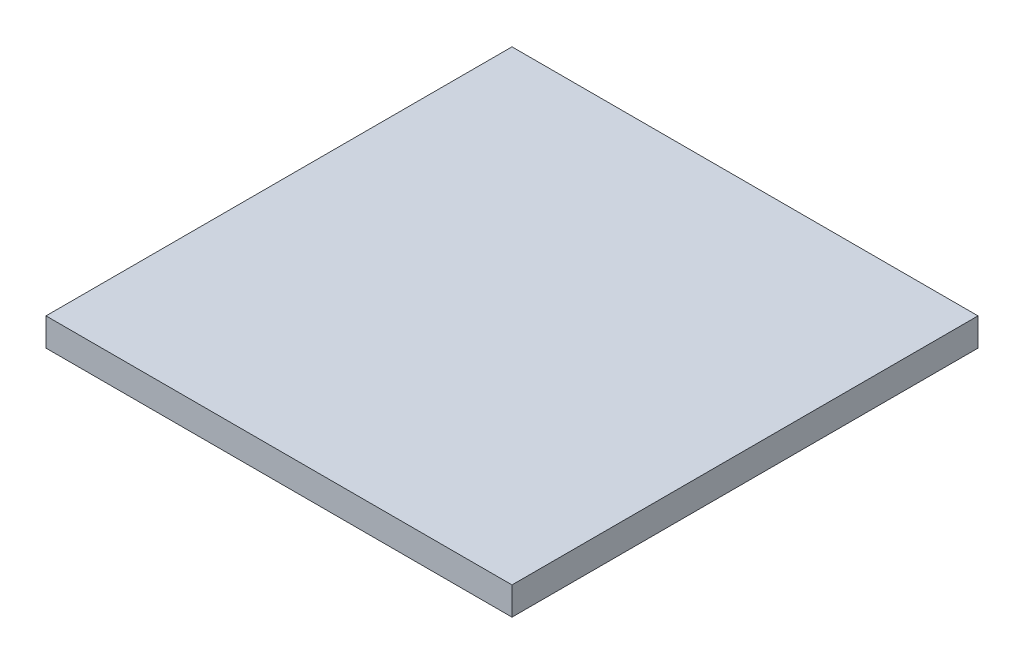
SolidWorks part; units mm, degrees
ref_plane "Front Plane" through (0, 0, 0) normal (0, 0, 1) x (1, 0, 0)
ref_plane "Top Plane" through (0, 0, 0) normal (0, 1, 0) x (1, 0, 0)
ref_plane "Right Plane" through (0, 0, 0) normal (1, 0, 0) x (0, 0, -1)
sketch "Sketch1" plane through (0, 0, 0) normal (0, 1, 0) x (1, 0, 0)
  line L1 (635, -635) -> (-635, -635)
  line L2 (635, -635) -> (635, 635)
  line L3 (635, 635) -> (-635, 635)
  line L4 (-635, -635) -> (-635, 635)
  line L5 (635, -635) -> (-635, 635) construction
  line L6 (635, 635) -> (-635, -635) construction
  point P0 (0, 0)
  dimension "D1" = 1270
  dimension "D2" = 1270
extrude "Boss-Extrude1" add sketch "Sketch1" along normal blind 76.2
